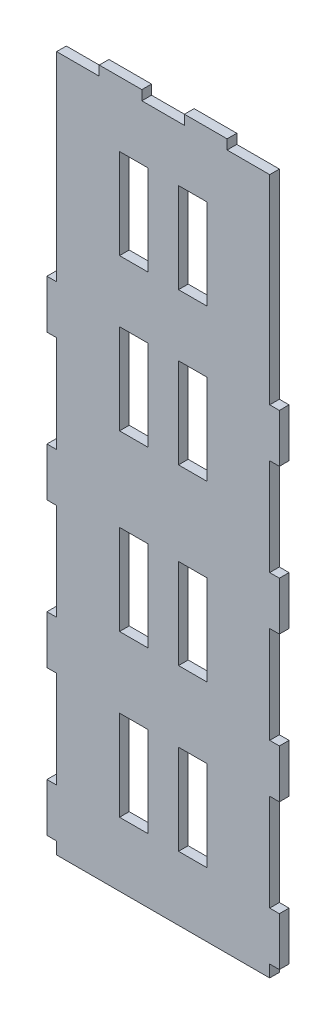
SolidWorks part; units mm, degrees
material "1060 Alloy"
ref_plane "Front Plane" through (0, 0, 0) normal (0, 0, 1) x (1, 0, 0)
ref_plane "Top Plane" through (0, 0, 0) normal (0, 1, 0) x (1, 0, 0)
ref_plane "Right Plane" through (0, 0, 0) normal (1, 0, 0) x (0, 0, -1)
sketch "Sketch1" plane through (0, 0, 0) normal (0, 0, 1) x (1, 0, 0)
  line L0 (6.4, 64.344) -> (-11.2, 64.344)
  line L2 (-64, -226.9963) -> (24, -226.9963)
  line L4 (-64, 60.344) -> (-64, -21.9963)
  line L5 (-64, -21.9963) -> (-68, -21.9963)
  line L6 (-68, -21.9963) -> (-68, -41.9963)
  line L7 (-68, -41.9963) -> (-64, -41.9963)
  line L8 (-64, -41.9963) -> (-64, -81.9963)
  line L9 (-64, -81.9963) -> (-68, -81.9963)
  line L10 (-68, -81.9963) -> (-68, -101.9963)
  line L11 (-68, -101.9963) -> (-64, -101.9963)
  line L12 (-64, -101.9963) -> (-64, -141.9963)
  line L13 (-64, -141.9963) -> (-68, -141.9963)
  line L14 (-68, -141.9963) -> (-68, -161.9963)
  line L15 (-68, -161.9963) -> (-64, -161.9963)
  line L16 (-64, -161.9963) -> (-64, -201.9963)
  line L17 (-64, -201.9963) -> (-68, -201.9963)
  line L18 (-68, -201.9963) -> (-68, -221.9963)
  line L19 (-68, -221.9963) -> (-64, -221.9963)
  line L20 (-64, -221.9963) -> (-64, -226.9963)
  line L21 (-20, 64.344) -> (-20, -226.9963) construction
  line L22 (24, -221.9963) -> (24, -226.9963)
  line L23 (28, -221.9963) -> (24, -221.9963)
  line L24 (28, -201.9963) -> (28, -221.9963)
  line L25 (24, -201.9963) -> (28, -201.9963)
  line L26 (24, -161.9963) -> (24, -201.9963)
  line L27 (28, -161.9963) -> (24, -161.9963)
  line L28 (28, -141.9963) -> (28, -161.9963)
  line L29 (24, -141.9963) -> (28, -141.9963)
  line L30 (24, -101.9963) -> (24, -141.9963)
  line L31 (28, -101.9963) -> (24, -101.9963)
  line L32 (28, -81.9963) -> (28, -101.9963)
  line L33 (24, -81.9963) -> (28, -81.9963)
  line L34 (24, -41.9963) -> (24, -81.9963)
  line L35 (28, -41.9963) -> (24, -41.9963)
  line L36 (28, -21.9963) -> (28, -41.9963)
  line L37 (24, -21.9963) -> (28, -21.9963)
  line L38 (24, 60.344) -> (24, -21.9963)
  line L39 (6.4, 64.344) -> (6.4, 60.344)
  line L40 (6.4, 60.344) -> (24, 60.344)
  line L41 (-11.2, 64.344) -> (-11.2, 60.344)
  line L42 (-11.2, 60.344) -> (-28.8, 60.344)
  line L43 (-28.8, 60.344) -> (-28.8, 64.344)
  line L44 (-60, 64.344) -> (4, 64.344) construction
  line L45 (-46.4, 64.344) -> (-46.4, 60.344)
  line L46 (-46.4, 60.344) -> (-64, 60.344)
  line L47 (-28.8, 64.344) -> (-46.4, 64.344)
  line L48 (-38.0163, -200.5092) -> (-26.3404, -200.5092)
  line L49 (-1.9837, 37.6052) -> (-13.6596, 37.6052)
  line L50 (-1.9837, 37.6052) -> (-1.9837, 0.3626)
  line L51 (-1.9837, 0.3626) -> (-13.6596, 0.3626)
  line L52 (-13.6596, 37.6052) -> (-13.6596, 0.3626)
  line L53 (-1.9837, -25.0654) -> (-13.6596, -25.0654)
  line L54 (-1.9837, -25.0654) -> (-1.9837, -62.3081)
  line L55 (-1.9837, -62.3081) -> (-13.6596, -62.3081)
  line L56 (-13.6596, -25.0654) -> (-13.6596, -62.3081)
  line L57 (-1.9837, -96.8392) -> (-13.6596, -96.8392)
  line L58 (-1.9837, -96.8392) -> (-1.9837, -134.0818)
  line L59 (-1.9837, -134.0818) -> (-13.6596, -134.0818)
  line L60 (-13.6596, -96.8392) -> (-13.6596, -134.0818)
  line L61 (-1.9837, -163.2666) -> (-13.6596, -163.2666)
  line L62 (-1.9837, -163.2666) -> (-1.9837, -200.5092)
  line L63 (-1.9837, -200.5092) -> (-13.6596, -200.5092)
  line L64 (-13.6596, -163.2666) -> (-13.6596, -200.5092)
  line L65 (-26.3404, -163.2666) -> (-26.3404, -200.5092)
  line L66 (-38.0163, -163.2666) -> (-26.3404, -163.2666)
  line L67 (-38.0163, -163.2666) -> (-38.0163, -200.5092)
  line L68 (-38.0163, -134.0818) -> (-26.3404, -134.0818)
  line L69 (-26.3404, -96.8392) -> (-26.3404, -134.0818)
  line L70 (-38.0163, -96.8392) -> (-26.3404, -96.8392)
  line L71 (-38.0163, -96.8392) -> (-38.0163, -134.0818)
  line L72 (-38.0163, -62.3081) -> (-26.3404, -62.3081)
  line L73 (-26.3404, -25.0654) -> (-26.3404, -62.3081)
  line L74 (-38.0163, -25.0654) -> (-26.3404, -25.0654)
  line L75 (-38.0163, -25.0654) -> (-38.0163, -62.3081)
  line L76 (-38.0163, 0.3626) -> (-26.3404, 0.3626)
  line L77 (-26.3404, 37.6052) -> (-26.3404, 0.3626)
  line L78 (-38.0163, 37.6052) -> (-26.3404, 37.6052)
  line L79 (-38.0163, 37.6052) -> (-38.0163, 0.3626)
  dimension "D1" = 4
  dimension "D2" = 5
  dimension "D3" = 20
  dimension "D4" = 40
  dimension "D5" = 4
  dimension "D6" = 88
  dimension "D7" = 291.3402
extrude "Boss-Extrude1" add sketch "Sketch1" along normal blind 4
